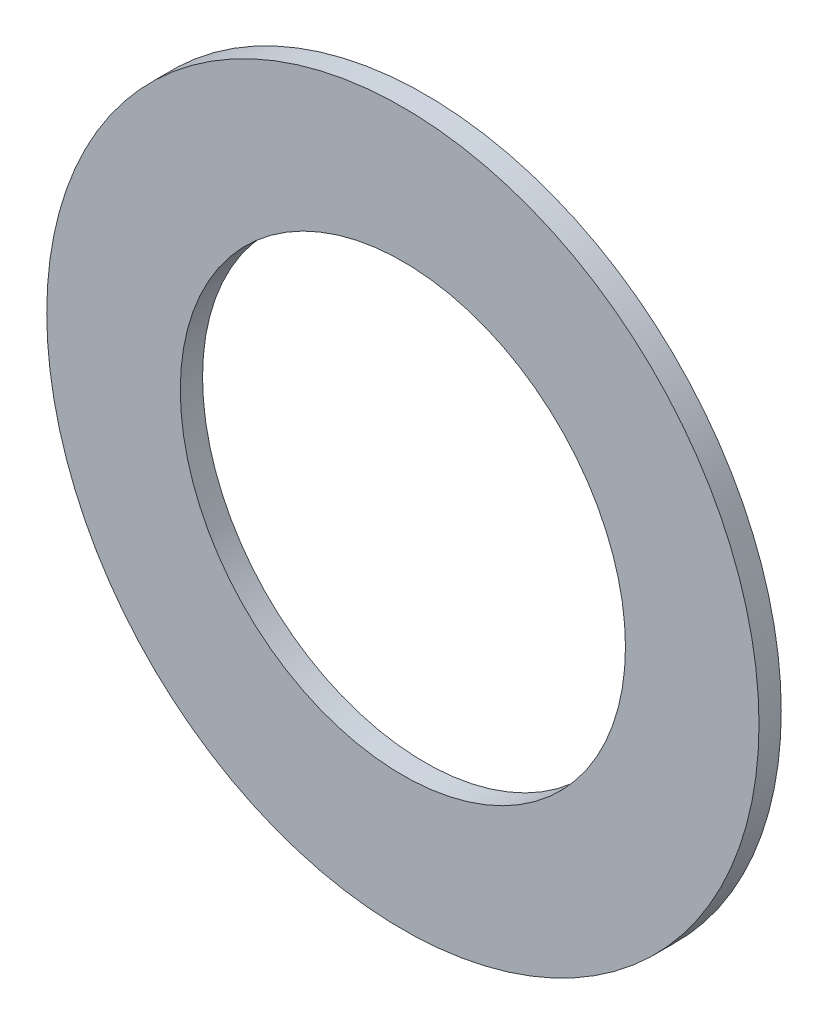
SolidWorks part; units mm, degrees
material "Stainless Steel (ferritic)"
ref_plane "Front Plane" through (0, 0, 0) normal (0, 0, 1) x (1, 0, 0)
ref_plane "Top Plane" through (0, 0, 0) normal (0, 1, 0) x (1, 0, 0)
ref_plane "Right Plane" through (0, 0, 0) normal (1, 0, 0) x (0, 0, -1)
sketch "Sketch1" plane through (0, 0, 0) normal (0, 0, 1) x (1, 0, 0)
  circle A0 centre (0, 0) radius 5
  circle A1 centre (0, 0) radius 8
  dimension "D1" = 10
  dimension "D2" = 16
extrude "Boss-Extrude1" add sketch "Sketch1" along normal blind 0.5
